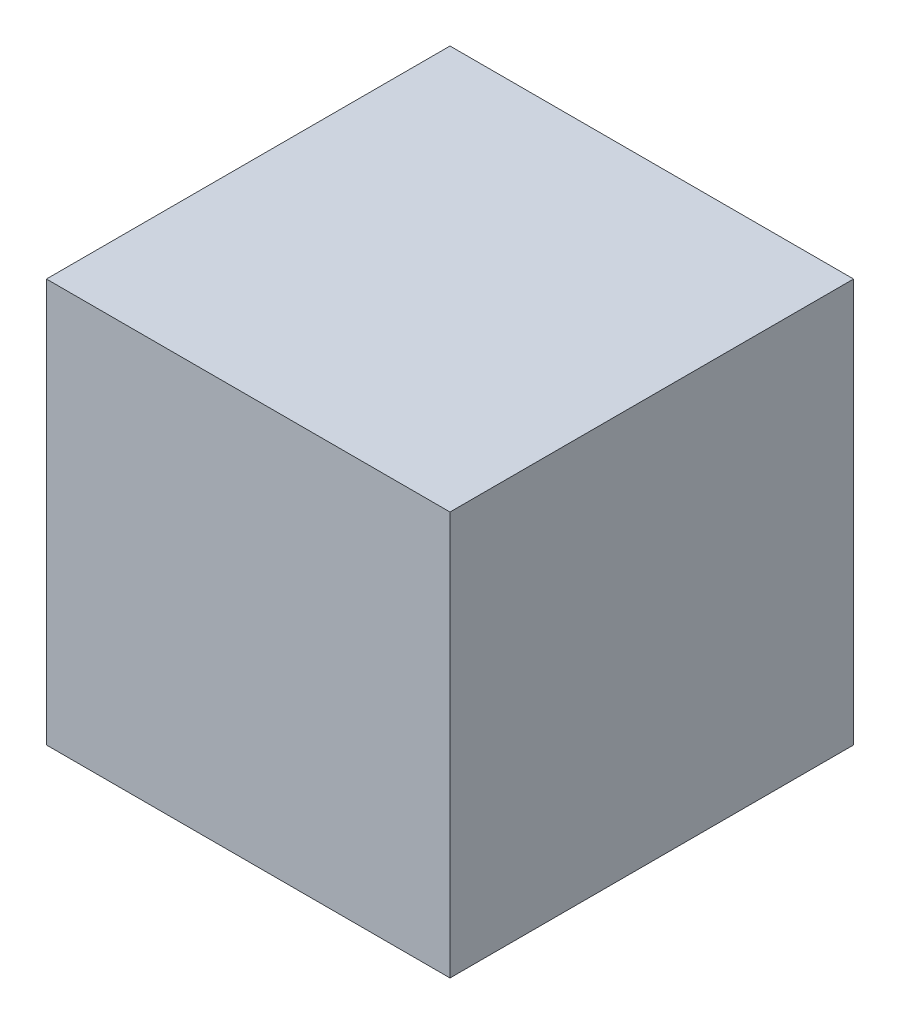
SolidWorks part; units mm, degrees
ref_plane "Front Plane" through (0, 0, 0) normal (0, 0, 1) x (1, 0, 0)
ref_plane "Top Plane" through (0, 0, 0) normal (0, 1, 0) x (1, 0, 0)
ref_plane "Right Plane" through (0, 0, 0) normal (1, 0, 0) x (0, 0, -1)
sketch "Szkic1" plane through (0, 0, 0) normal (0, 0, 1) x (1, 0, 0)
  line L1 (-50, -50) -> (50, -50)
  line L2 (-50, -50) -> (-50, 50)
  line L3 (-50, 50) -> (50, 50)
  line L4 (50, -50) -> (50, 50)
  line L5 (-50, -50) -> (50, 50) construction
  line L6 (-50, 50) -> (50, -50) construction
  point P0 (0, 0)
  dimension "D1" = 100
  dimension "D2" = 100
extrude "Dodanie-wyciągnięcie1" add sketch "Szkic1" along normal blind 100
shell "Skorupa2" thickness 10
